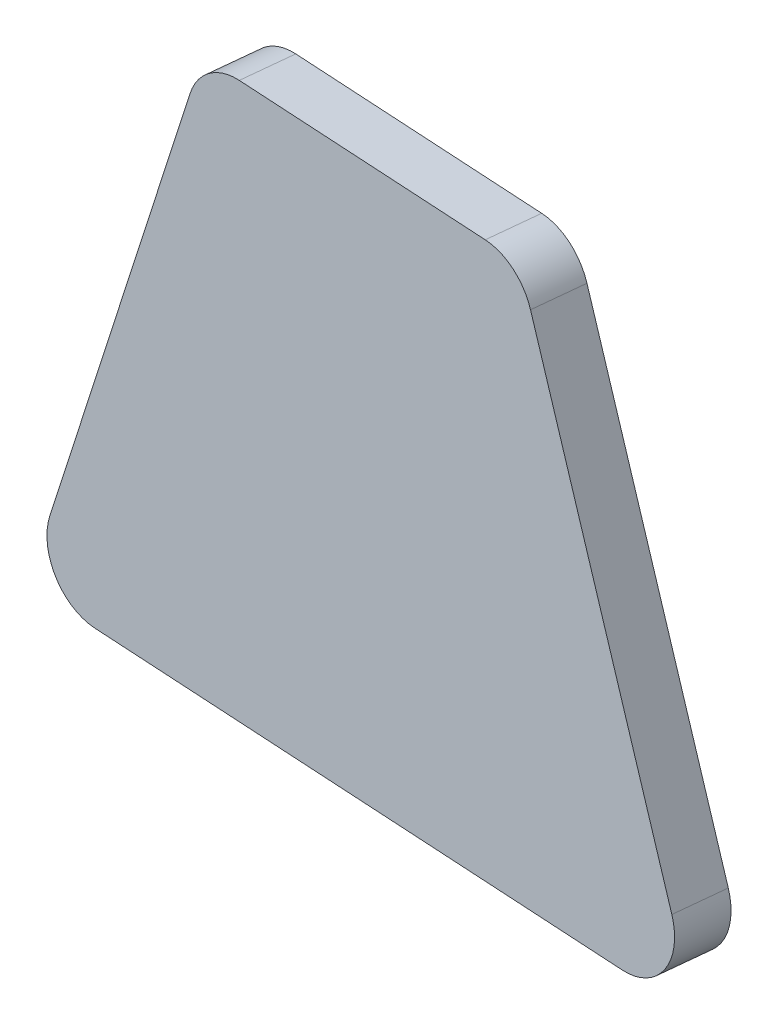
SolidWorks part; units mm, degrees
material "AISI 4130 Steel, normalized at 870C"
ref_plane "Top" through (0, 0, 0) normal (0, 0, 1) x (1, 0, 0)
ref_plane "Right" through (0, 0, 0) normal (0, 1, 0) x (1, 0, 0)
ref_plane "Front" through (0, 0, 0) normal (1, 0, 0) x (0, 0, -1)
ref_plane "Plane1" through (-8.0734, 5.2406, 134.3789) normal (-0.0599, 0.0389, 0.9974) x (0.9982, 0.0023, 0.0599)
sketch "Sketch1" plane through (-8.0734, 5.2406, 134.3789) normal (-0.0599, 0.0389, 0.9974) x (0.9982, 0.0023, 0.0599)
  line L0 (7.6114, 519.3198) -> (1.7395, 500.2698) construction
  line L1 (-95.6717, 184.2397) -> (7.6114, 519.3198) construction
  line L2 (7.6114, 519.3198) -> (15.1208, 500.2698) construction
  line L3 (7.6114, 519.3198) -> (138.041, 188.4454) construction
  line L4 (16.486, 500.2698) -> (26.4985, 474.8698)
  line L5 (26.4985, 474.8698) -> (-7.4186, 474.8698)
  line L6 (-7.4186, 474.8698) -> (0.4106, 500.2698)
  line L7 (0.4106, 500.2698) -> (16.486, 500.2698)
  dimension "D1" = 19.05
  dimension "D2" = 1.27
  dimension "D3" = 1.27
  dimension "D4" = 25.4
extrude "Boss-Extrude1" add sketch "Sketch1" along normal blind 2.54
fillet "Fillet1" radius 2.54 4 edges at (-7.7396, 505.1808, 116.1751) (8.3068, 505.2184, 117.1377) (18.3014, 479.861, 118.7271) (-15.5547, 479.7818, 116.6962)
